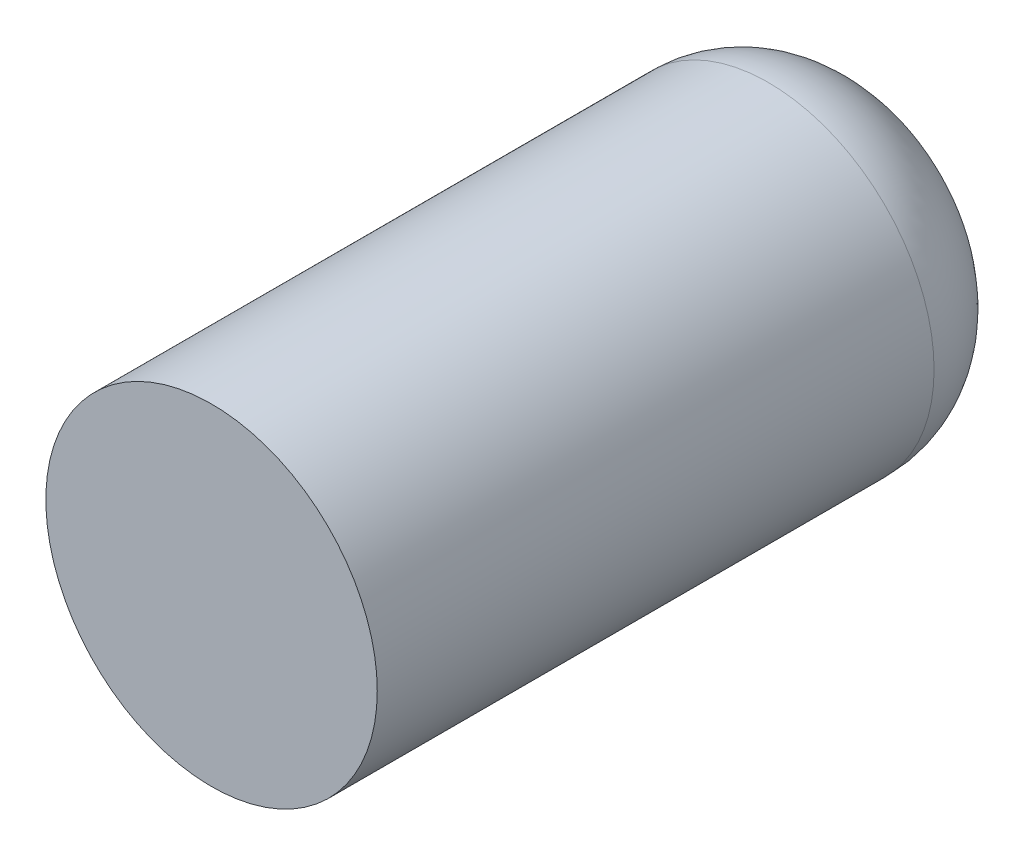
SolidWorks part; units mm, degrees
ref_plane "Front Plane" through (0, 0, 0) normal (0, 0, 1) x (1, 0, 0)
ref_plane "Top Plane" through (0, 0, 0) normal (0, 1, 0) x (1, 0, 0)
ref_plane "Right Plane" through (0, 0, 0) normal (1, 0, 0) x (0, 0, -1)
sketch "Sketch1" plane through (0, 0, 0) normal (0, 0, 1) x (1, 0, 0)
  circle A0 centre (0, 0) radius 7.9375
  dimension "D1" = 15.875
extrude "Boss-Extrude1" add sketch "Sketch1" along normal blind 31.75
fillet "Fillet1" radius 5.08 1 edges at (7.9375, 0, 0)
